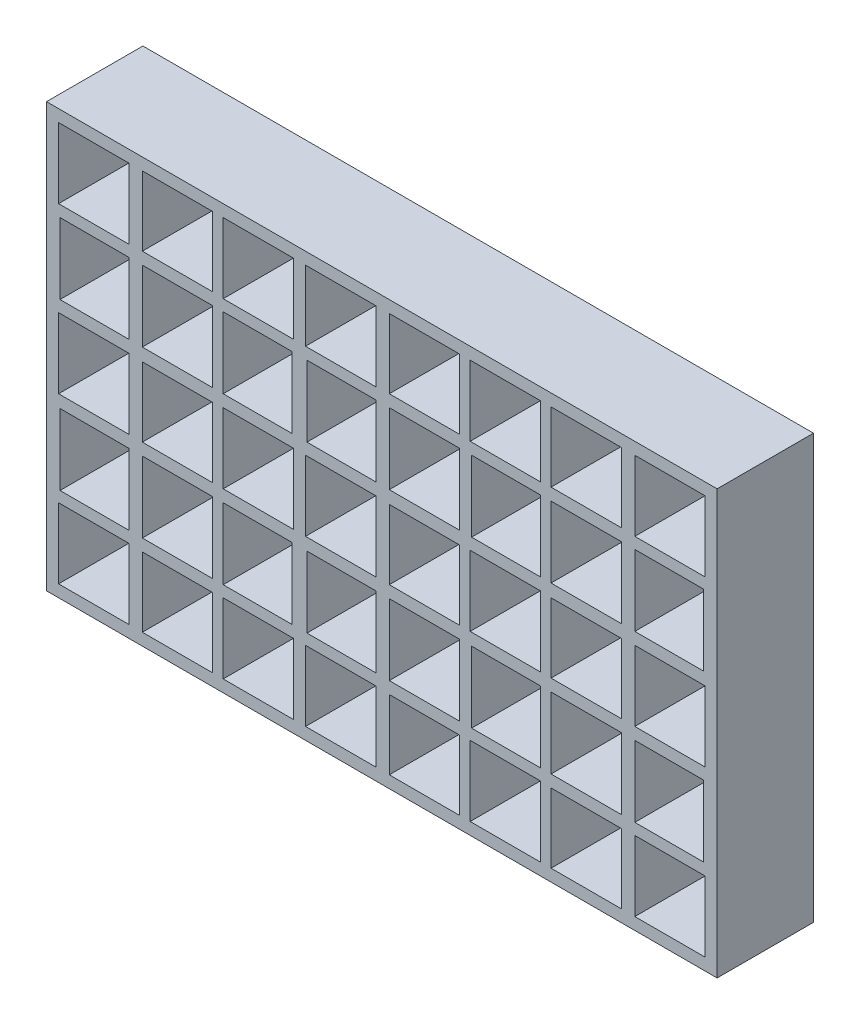
SolidWorks part; units mm, degrees
ref_plane "Front Plane" through (0, 0, 0) normal (0, 0, 1) x (1, 0, 0)
ref_plane "Top Plane" through (0, 0, 0) normal (0, 1, 0) x (1, 0, 0)
ref_plane "Right Plane" through (0, 0, 0) normal (1, 0, 0) x (0, 0, -1)
sketch "Sketch1" plane through (0, 0, 0) normal (0, 0, 1) x (1, 0, 0)
  line L0 (170, 0) -> (-170, 0) construction
  line L1 (0, 110) -> (0, -110) construction
  line L2 (170, 41) -> (-170, 41) construction
  line L3 (170, 82) -> (-170, 82) construction
  line L4 (170, -41) -> (-170, -41) construction
  line L5 (170, -82) -> (-170, -82) construction
  line L6 (-20.5, 110) -> (-20.5, -110) construction
  line L7 (-61.5, 110) -> (-61.5, -110) construction
  line L8 (-102.5, 110) -> (-102.5, -110) construction
  line L9 (20.5, 110) -> (20.5, -110) construction
  line L10 (61.5, 110) -> (61.5, -110) construction
  line L11 (102.5, 110) -> (102.5, -110) construction
  line L12 (-143.5, 110) -> (-143.5, -110) construction
  line L13 (143.5, 110) -> (143.5, -110) construction
  line L14 (126, 23.5) -> (160.2776, 23.5)
  line L15 (-167, 105.5) -> (167, 105.5)
  line L16 (-167, 105.5) -> (-167, -105.5)
  line L17 (-167, -105.5) -> (167, -105.5)
  line L18 (167, 105.5) -> (167, -105.5)
  line L21 (126, 64.5) -> (161, 64.5)
  line L22 (126, 64.5) -> (126, 99.5)
  line L23 (126, 99.5) -> (161, 99.5)
  line L24 (161, 64.5) -> (161, 99.5)
  line L27 (126, 23.5) -> (126, 58.8612)
  line L28 (126, 58.8612) -> (160.2776, 58.8612)
  line L29 (160.2776, 23.5) -> (160.2776, 58.8612)
  line L30 (79, 99.5) -> (44, 99.5)
  line L31 (44, 64.5) -> (44, 99.5)
  line L32 (79, 64.5) -> (44, 64.5)
  line L33 (79, 64.5) -> (79, 99.5)
  line L34 (79, 23.5) -> (79, 58.8612)
  line L35 (79, 58.8612) -> (44.7224, 58.8612)
  line L36 (44.7224, 23.5) -> (44.7224, 58.8612)
  line L37 (79, 23.5) -> (44.7224, 23.5)
  line L38 (84.2776, 64.8612) -> (119.2776, 64.8612)
  line L39 (84.2776, 64.8612) -> (84.2776, 99.5)
  line L40 (84.2776, 99.5) -> (119.2776, 99.5)
  line L41 (119.2776, 64.8612) -> (119.2776, 99.5)
  line L42 (84.2776, 23.5) -> (119.2776, 23.5)
  line L43 (84.2776, 23.5) -> (84.2776, 58.8612)
  line L44 (84.2776, 58.8612) -> (119.2776, 58.8612)
  line L45 (119.2776, 23.5) -> (119.2776, 58.8612)
  line L46 (126, -23.5) -> (126, -58.8612)
  line L47 (126, -58.8612) -> (160.2776, -58.8612)
  line L48 (160.2776, -23.5) -> (160.2776, -58.8612)
  line L49 (126, -23.5) -> (160.2776, -23.5)
  line L50 (84.2776, -23.5) -> (84.2776, -58.8612)
  line L51 (84.2776, -58.8612) -> (119.2776, -58.8612)
  line L52 (119.2776, -23.5) -> (119.2776, -58.8612)
  line L53 (84.2776, -23.5) -> (119.2776, -23.5)
  line L54 (79, -23.5) -> (44.7224, -23.5)
  line L55 (44.7224, -23.5) -> (44.7224, -58.8612)
  line L56 (79, -58.8612) -> (44.7224, -58.8612)
  line L57 (79, -23.5) -> (79, -58.8612)
  line L58 (79, -64.5) -> (79, -99.5)
  line L59 (79, -64.5) -> (44, -64.5)
  line L60 (44, -64.5) -> (44, -99.5)
  line L61 (79, -99.5) -> (44, -99.5)
  line L62 (84.2776, -64.8612) -> (84.2776, -99.5)
  line L63 (84.2776, -99.5) -> (119.2776, -99.5)
  line L64 (119.2776, -64.8612) -> (119.2776, -99.5)
  line L65 (84.2776, -64.8612) -> (119.2776, -64.8612)
  line L66 (126, -99.5) -> (161, -99.5)
  line L67 (161, -64.5) -> (161, -99.5)
  line L68 (126, -64.5) -> (161, -64.5)
  line L69 (126, -64.5) -> (126, -99.5)
  line L70 (-126, -64.5) -> (-126, -99.5)
  line L71 (-126, -64.5) -> (-161, -64.5)
  line L72 (-161, -64.5) -> (-161, -99.5)
  line L73 (-126, -99.5) -> (-161, -99.5)
  line L74 (-84.2776, -64.8612) -> (-119.2776, -64.8612)
  line L75 (-119.2776, -64.8612) -> (-119.2776, -99.5)
  line L76 (-84.2776, -99.5) -> (-119.2776, -99.5)
  line L77 (-84.2776, -64.8612) -> (-84.2776, -99.5)
  line L78 (-79, -64.5) -> (-44, -64.5)
  line L79 (-44, -64.5) -> (-44, -99.5)
  line L80 (-79, -99.5) -> (-44, -99.5)
  line L81 (-79, -64.5) -> (-79, -99.5)
  line L82 (-79, -23.5) -> (-79, -58.8612)
  line L83 (-79, -58.8612) -> (-44.7224, -58.8612)
  line L84 (-44.7224, -23.5) -> (-44.7224, -58.8612)
  line L85 (-79, -23.5) -> (-44.7224, -23.5)
  line L86 (-84.2776, -23.5) -> (-119.2776, -23.5)
  line L87 (-119.2776, -23.5) -> (-119.2776, -58.8612)
  line L88 (-84.2776, -58.8612) -> (-119.2776, -58.8612)
  line L89 (-84.2776, -23.5) -> (-84.2776, -58.8612)
  line L90 (-126, -23.5) -> (-160.2776, -23.5)
  line L91 (-160.2776, -23.5) -> (-160.2776, -58.8612)
  line L92 (-126, -58.8612) -> (-160.2776, -58.8612)
  line L93 (-126, -23.5) -> (-126, -58.8612)
  line L94 (-126, 23.5) -> (-126, 58.8612)
  line L95 (-126, 58.8612) -> (-160.2776, 58.8612)
  line L96 (-160.2776, 23.5) -> (-160.2776, 58.8612)
  line L97 (-126, 23.5) -> (-160.2776, 23.5)
  line L98 (-84.2776, 23.5) -> (-84.2776, 58.8612)
  line L99 (-84.2776, 58.8612) -> (-119.2776, 58.8612)
  line L100 (-119.2776, 23.5) -> (-119.2776, 58.8612)
  line L101 (-84.2776, 23.5) -> (-119.2776, 23.5)
  line L102 (-79, 23.5) -> (-44.7224, 23.5)
  line L103 (-44.7224, 23.5) -> (-44.7224, 58.8612)
  line L104 (-79, 58.8612) -> (-44.7224, 58.8612)
  line L105 (-79, 23.5) -> (-79, 58.8612)
  line L106 (-79, 64.5) -> (-79, 99.5)
  line L107 (-79, 64.5) -> (-44, 64.5)
  line L108 (-44, 64.5) -> (-44, 99.5)
  line L109 (-79, 99.5) -> (-44, 99.5)
  line L110 (-84.2776, 64.8612) -> (-84.2776, 99.5)
  line L111 (-84.2776, 99.5) -> (-119.2776, 99.5)
  line L112 (-119.2776, 64.8612) -> (-119.2776, 99.5)
  line L113 (-84.2776, 64.8612) -> (-119.2776, 64.8612)
  line L114 (-126, 99.5) -> (-161, 99.5)
  line L115 (-161, 64.5) -> (-161, 99.5)
  line L116 (-126, 64.5) -> (-161, 64.5)
  line L117 (-126, 64.5) -> (-126, 99.5)
  line L118 (79, 17.5) -> (79, -17.5)
  line L119 (79, 17.5) -> (44, 17.5)
  line L120 (44, 17.5) -> (44, -17.5)
  line L121 (79, -17.5) -> (44, -17.5)
  line L122 (84.2776, 17.1388) -> (84.2776, -17.5)
  line L123 (84.2776, -17.5) -> (119.2776, -17.5)
  line L124 (119.2776, 17.1388) -> (119.2776, -17.5)
  line L125 (84.2776, 17.1388) -> (119.2776, 17.1388)
  line L126 (126, -17.5) -> (161, -17.5)
  line L127 (161, 17.5) -> (161, -17.5)
  line L128 (126, 17.5) -> (161, 17.5)
  line L129 (126, 17.5) -> (126, -17.5)
  line L130 (-126, 17.5) -> (-126, -17.5)
  line L131 (-126, 17.5) -> (-161, 17.5)
  line L132 (-161, 17.5) -> (-161, -17.5)
  line L133 (-126, -17.5) -> (-161, -17.5)
  line L134 (-84.2776, 17.1388) -> (-119.2776, 17.1388)
  line L135 (-119.2776, 17.1388) -> (-119.2776, -17.5)
  line L136 (-84.2776, -17.5) -> (-119.2776, -17.5)
  line L137 (-84.2776, 17.1388) -> (-84.2776, -17.5)
  line L138 (-79, 17.5) -> (-44, 17.5)
  line L139 (-44, 17.5) -> (-44, -17.5)
  line L140 (-79, -17.5) -> (-44, -17.5)
  line L141 (-79, 17.5) -> (-79, -17.5)
  line L142 (-3, 99.5) -> (-38, 99.5)
  line L143 (-38, 64.5) -> (-38, 99.5)
  line L144 (-3, 64.5) -> (-38, 64.5)
  line L145 (-3, 64.5) -> (-3, 99.5)
  line L146 (-3, 23.5) -> (-3, 58.8612)
  line L147 (-3, 58.8612) -> (-37.2776, 58.8612)
  line L148 (-37.2776, 23.5) -> (-37.2776, 58.8612)
  line L149 (-3, 23.5) -> (-37.2776, 23.5)
  line L150 (-3, 17.5) -> (-3, -17.5)
  line L151 (-3, 17.5) -> (-38, 17.5)
  line L152 (-38, 17.5) -> (-38, -17.5)
  line L153 (-3, -17.5) -> (-38, -17.5)
  line L154 (-3, -23.5) -> (-37.2776, -23.5)
  line L155 (-37.2776, -23.5) -> (-37.2776, -58.8612)
  line L156 (-3, -58.8612) -> (-37.2776, -58.8612)
  line L157 (-3, -23.5) -> (-3, -58.8612)
  line L158 (-3, -64.5) -> (-3, -99.5)
  line L159 (-3, -64.5) -> (-38, -64.5)
  line L160 (-38, -64.5) -> (-38, -99.5)
  line L161 (-3, -99.5) -> (-38, -99.5)
  line L162 (38.7224, -64.8612) -> (3.7224, -64.8612)
  line L163 (3.7224, -64.8612) -> (3.7224, -99.5)
  line L164 (38.7224, -99.5) -> (3.7224, -99.5)
  line L165 (38.7224, -64.8612) -> (38.7224, -99.5)
  line L166 (38.7224, -23.5) -> (3.7224, -23.5)
  line L167 (3.7224, -23.5) -> (3.7224, -58.8612)
  line L168 (38.7224, -58.8612) -> (3.7224, -58.8612)
  line L169 (38.7224, -23.5) -> (38.7224, -58.8612)
  line L170 (38.7224, 17.1388) -> (3.7224, 17.1388)
  line L171 (3.7224, 17.1388) -> (3.7224, -17.5)
  line L172 (38.7224, -17.5) -> (3.7224, -17.5)
  line L173 (38.7224, 17.1388) -> (38.7224, -17.5)
  line L174 (38.7224, 23.5) -> (38.7224, 58.8612)
  line L175 (38.7224, 58.8612) -> (3.7224, 58.8612)
  line L176 (3.7224, 23.5) -> (3.7224, 58.8612)
  line L177 (38.7224, 23.5) -> (3.7224, 23.5)
  line L178 (38.7224, 64.8612) -> (38.7224, 99.5)
  line L179 (38.7224, 99.5) -> (3.7224, 99.5)
  line L180 (3.7224, 64.8612) -> (3.7224, 99.5)
  line L181 (38.7224, 64.8612) -> (3.7224, 64.8612)
  point P3 (0, 0)
  point P30 (0, 0)
  point P35 (142.7776, 82)
  point P196 (0, 0)
  point P197 (0, 0)
  point P198 (101.7263, 110)
  point P199 (142.7776, 110)
  point P200 (0, 0)
  point P201 (0, 0)
  dimension "D2" = 35
  dimension "D3" = 211
  dimension "D5" = 41
  dimension "D8" = 41
  dimension "D15" = 334
  dimension "D16" = 35
extrude "Boss-Extrude1" add sketch "Sketch1" along normal blind 45
sketch "Sketch2" plane through (0, 0, 0) normal (0, 0, -1) x (-1, 0, 0)
  line L1 (-167, 105.5) -> (167, 105.5)
  line L2 (-167, 105.5) -> (-167, -105.5)
  line L3 (-167, -105.5) -> (167, -105.5)
  line L4 (167, 105.5) -> (167, -105.5)
  line L5 (-167, 105.5) -> (167, -105.5) construction
  line L6 (-167, -105.5) -> (167, 105.5) construction
  point P0 (0, 0)
extrude "Boss-Extrude2" add sketch "Sketch2" along normal blind 3
